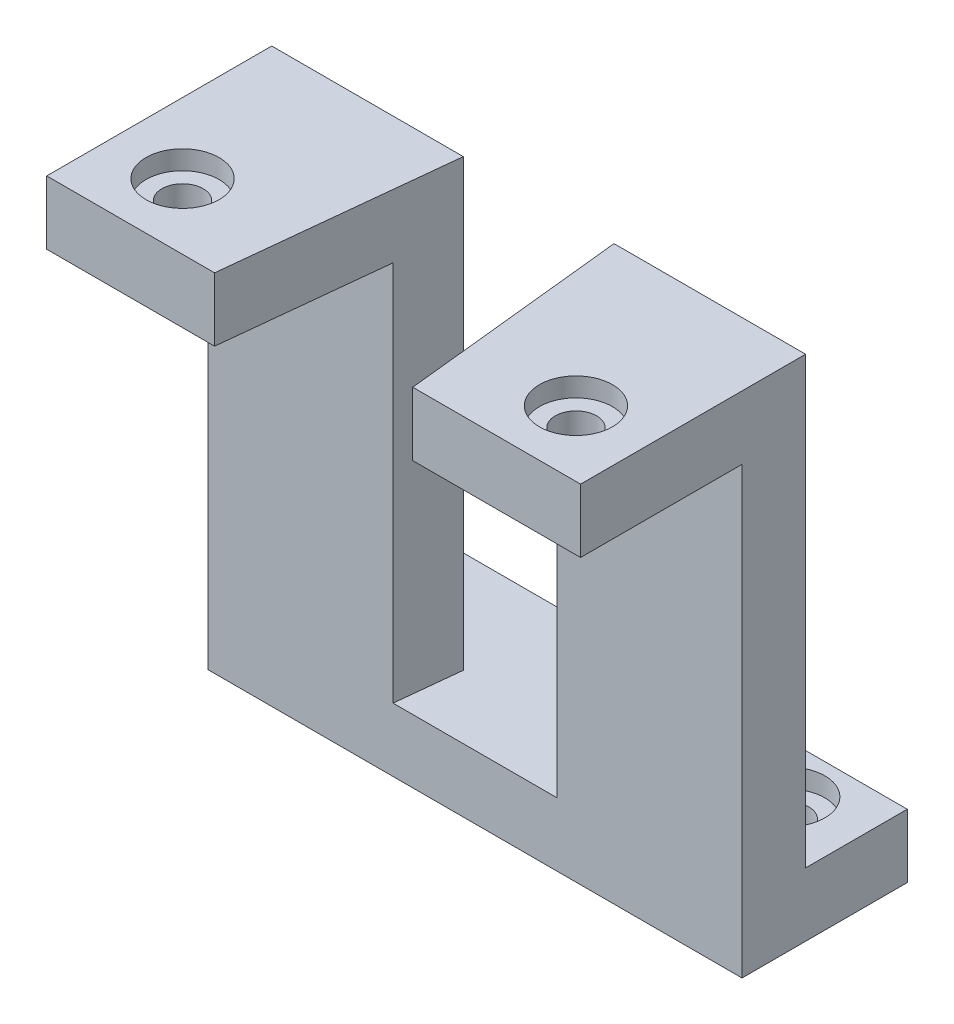
SolidWorks part; units mm, degrees
ref_plane "Front Plane" through (0, 0, 0) normal (0, 0, 1) x (1, 0, 0)
ref_plane "Top Plane" through (0, 0, 0) normal (0, 1, 0) x (1, 0, 0)
ref_plane "Right Plane" through (0, 0, 0) normal (1, 0, 0) x (0, 0, -1)
sketch "Sketch2" plane through (0, 0, 0) normal (0, 1, 0) x (1, 0, 0)
  line L0 (0, 4.9772) -> (0, -3.8306) construction
  line L2 (-21, 4.9772) -> (-21, -4.9772)
  line L3 (-21, -4.9772) -> (21, -4.9772)
  line L4 (21, 4.9772) -> (21, -4.9772)
  line L5 (-21, 4.9772) -> (21, -4.9772) construction
  line L6 (-21, -4.9772) -> (21, 4.9772) construction
  line L7 (-21, 4.9772) -> (-21, 12.7244)
  line L8 (-21, 12.7244) -> (21, 12.7244)
  line L9 (21, 12.7244) -> (21, 4.9772)
  circle A0 centre (-15.475, 0.1824) radius 1.625
  circle A1 centre (15.475, 0.1824) radius 1.625
  point P0 (0, 0)
  point P10 (-17.1, 0.1824)
  dimension "D2" = 3.25
  dimension "D1" = 42
  dimension "D3" = 3.9
extrude "Boss-Extrude1" add sketch "Sketch2" along normal blind 10
sketch "Sketch3" plane through (0, 10, 0) normal (0, 1, 0) x (1, 0, 0)
  circle A0 centre (-15.475, 0.1824) radius 2.875
  circle A1 centre (15.475, 0.1824) radius 2.875
  dimension "D1" = 5.75
  dimension "D2" = 5.75
extrude "Cut-Extrude1" cut sketch "Sketch3" against normal blind 1.5
sketch "Sketch4" plane through (0, 0, 0) normal (0, -1, 0) x (1, 0, 0)
  line L0 (21, 4.9772) -> (21, -12.7244) construction
  line L1 (-21, -12.7244) -> (21, -12.7244)
  line L2 (-21, -12.7244) -> (-21, -7.7244)
  line L3 (-21, -7.7244) -> (21, -7.7244)
  line L4 (21, -12.7244) -> (21, -7.7244)
  dimension "D1" = 5
extrude "Boss-Extrude2" add sketch "Sketch4" along normal blind 30
sketch "Sketch5" plane through (0, 0, -12.7244) normal (0, 0, -1) x (-1, 0, 0)
  line L0 (21, 10) -> (21, -30) construction
  line L1 (-21, -30) -> (21, -30)
  line L2 (-21, -30) -> (-21, -25)
  line L3 (-21, -25) -> (21, -25)
  line L4 (21, -30) -> (21, -25)
  dimension "D1" = 5
extrude "Boss-Extrude3" add sketch "Sketch5" along normal blind 8
sketch "Sketch6" plane through (-21, 0, 0) normal (-1, 0, 0) x (0, 0, 1)
  line L0 (4.9772, 10) -> (4.9772, 0) construction
  line L1 (-7.7244, 0) -> (4.9772, 0)
  line L2 (-7.7244, 0) -> (-7.7244, 5)
  line L3 (-7.7244, 5) -> (4.9772, 5)
  line L4 (4.9772, 0) -> (4.9772, 5)
  dimension "D1" = 5
extrude "Cut-Extrude2" cut sketch "Sketch6" against normal up to next
sketch "Sketch8" plane through (0, -25, 0) normal (0, 1, 0) x (1, 0, 0)
  line L0 (-15.475, 0.1824) -> (-15.475, 16.885) construction
  line L1 (0, -4.9772) -> (0, 9.5022) construction
  line L2 (-21, -4.9772) -> (21, -4.9772) construction
  circle A0 centre (-15.475, 16.885) radius 1.625
  circle A1 centre (15.475, 16.885) radius 1.625
  dimension "D1" = 3.25
extrude "Cut-Extrude3" cut sketch "Sketch8" against normal up to next
sketch "Sketch9" plane through (0, -25, 0) normal (0, 1, 0) x (1, 0, 0)
  circle A0 centre (-15.475, 16.885) radius 2.875
  circle A1 centre (15.475, 16.885) radius 2.875
  dimension "D1" = 5.75
  dimension "D2" = 5.75
extrude "Cut-Extrude4" cut sketch "Sketch9" against normal blind 1.5
sketch "Sketch11" plane through (0, 10, 0) normal (0, 1, 0) x (1, 0, 0)
  line L0 (0, -4.9772) -> (0, 8.1125) construction
  line L1 (-21, -4.9772) -> (21, -4.9772) construction
  line L2 (-7.7953, -4.9772) -> (-5.9279, 12.7244)
  line L3 (21, 12.7244) -> (-21, 12.7244) construction
  line L4 (7.7953, -4.9772) -> (5.9279, 12.7244)
  line L5 (-5.9279, 12.7244) -> (5.9279, 12.7244)
  line L6 (-7.7953, -4.9772) -> (7.7953, -4.9772)
extrude "Cut-Extrude5" cut sketch "Sketch11" against normal up to surface (35 mm away) up to face at (-18.35, -25, -16.885)
